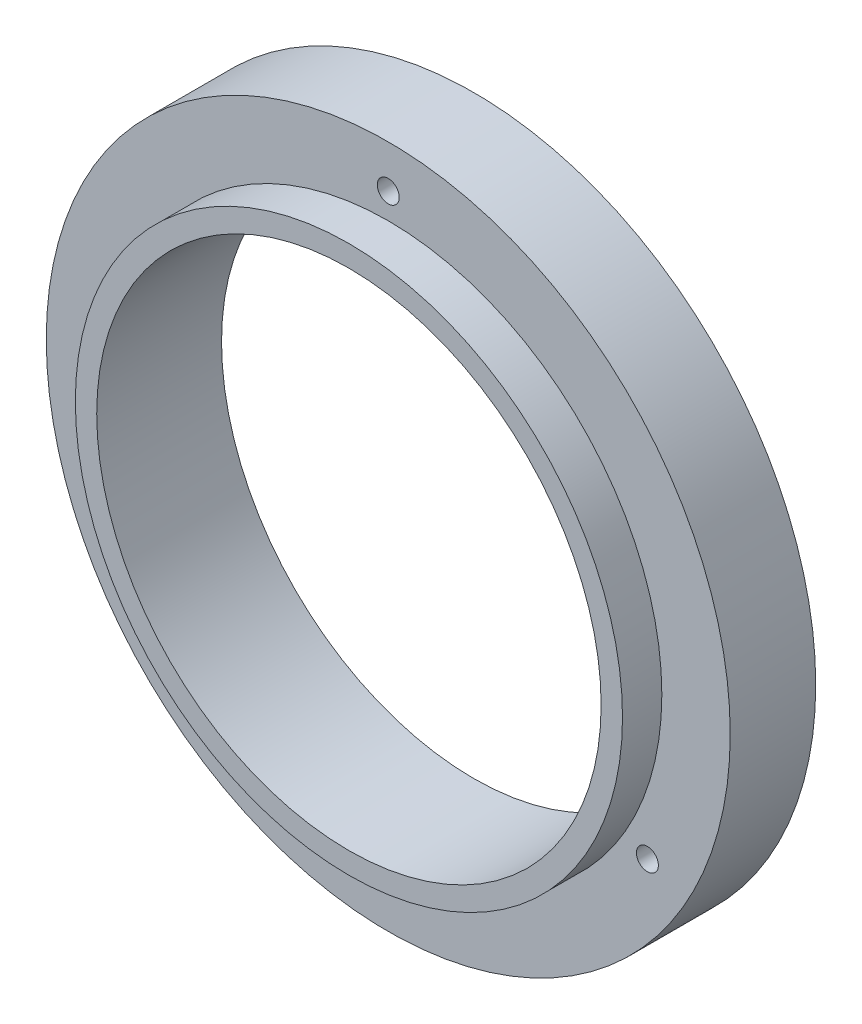
SolidWorks part; units mm, degrees
ref_plane "Front Plane" through (0, 0, 0) normal (0, 0, 1) x (1, 0, 0)
ref_plane "Top Plane" through (0, 0, 0) normal (0, 1, 0) x (1, 0, 0)
ref_plane "Right Plane" through (0, 0, 0) normal (1, 0, 0) x (0, 0, -1)
sketch "Sketch1" plane through (0, 0, 0) normal (0, 0, 1) x (1, 0, 0)
  circle A0 centre (0, 0) radius 50.8
  dimension "D1" = 101.6
extrude "Boss-Extrude1" add sketch "Sketch1" along normal blind 12.7
sketch "Sketch2" plane through (0, 0, 12.7) normal (0, 0, 1) x (1, 0, 0)
  circle A0 centre (0, 0) radius 40.64
  circle A1 centre (0, 0) radius 37.465
  dimension "D2" = 81.28
  dimension "D1" = 3.175
extrude "Boss-Extrude2" add sketch "Sketch2" along normal blind 5.842
sketch "Sketch4" plane through (0, 0, 12.7) normal (0, 0, 1) x (1, 0, 0)
  circle A0 centre (0, 0) radius 37.465
  dimension "D1" = 74.93
extrude "Cut-Extrude1" cut sketch "Sketch4" against normal through all
hole_wizard "CBORE for #4 Socket Head Cap Screw1" positions "Sketch7" profile "Sketch6" counterbore size "#4" standard "ANSI Inch"
sketch "Sketch7" plane through (0, 0, 0) normal (0, 0, -1) x (-1, 0, 0)
  point P0 (0, 44.45)
  dimension "D1" = 44.45
sketch "Sketch6" plane through (0, 44.45, 0) normal (1, 0, 0) x (0, 1, 0)
  line L0 (0, 0) -> (0, 13.8076)
  line L1 (0, 13.8076) -> (1.6319, 12.827)
  line L2 (1.6319, 12.827) -> (1.6319, 2.8448)
  line L3 (1.6319, 2.8448) -> (2.7788, 2.8448)
  line L4 (2.7788, 2.8448) -> (2.7788, 0)
  line L5 (2.7788, 0) -> (0, 0)
  line L10 (0, 13.8076) -> (-1.632, 12.827) construction
  line L11 (0, -6.35) -> (0, 107.95) construction
  dimension "Hole Dia." = 3.2639
  dimension "Hole Depth" = 12.827
  dimension "C'Bore Dia." = 5.5575
  dimension "C'Bore Depth" = 2.8448
  dimension "Drill Angle" = 118
pattern_circular "CirPattern1" count 3 over 360 about axis through (0, 0, 0) along (0, 0, 1) of "CBORE for #4 Socket Head Cap Screw1"
chamfer "Chamfer1" [suppressed] distance 3.175 angle 45
